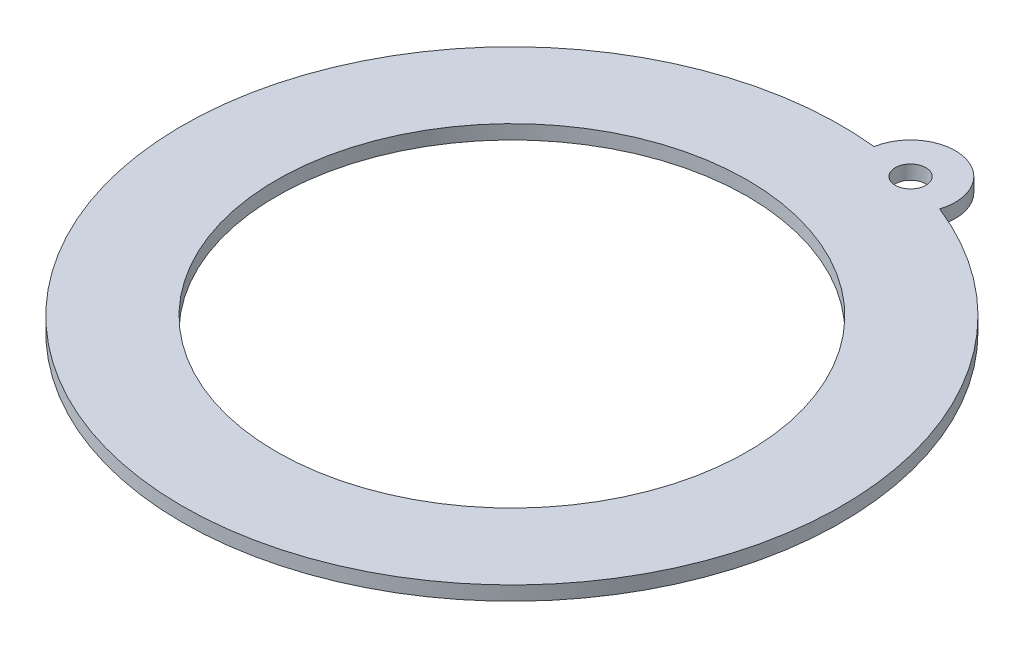
SolidWorks part; units mm, degrees
ref_plane "Front Plane" through (0, 0, 0) normal (0, 0, 1) x (1, 0, 0)
ref_plane "Top Plane" through (0, 0, 0) normal (0, 1, 0) x (1, 0, 0)
ref_plane "Right Plane" through (0, 0, 0) normal (1, 0, 0) x (0, 0, -1)
sketch "Sketch1" plane through (0, 0, 0) normal (0, 1, 0) x (1, 0, 0)
  circle A0 centre (0, 0) radius 50
  arc A1 (7.3355, 69.6146) -> (25.7448, 65.0938) centre (0, 0) ccw
  arc A2 (7.3355, 69.6146) -> (25.7448, 65.0938) centre (16.6939, 67.9802) cw
  circle A3 centre (16.6939, 67.9802) radius 3.25
  dimension "D1" = 70
  dimension "D2" = 100
  dimension "D3" = 9.5
extrude "Boss-Extrude1" add sketch "Sketch1" along normal blind 3
